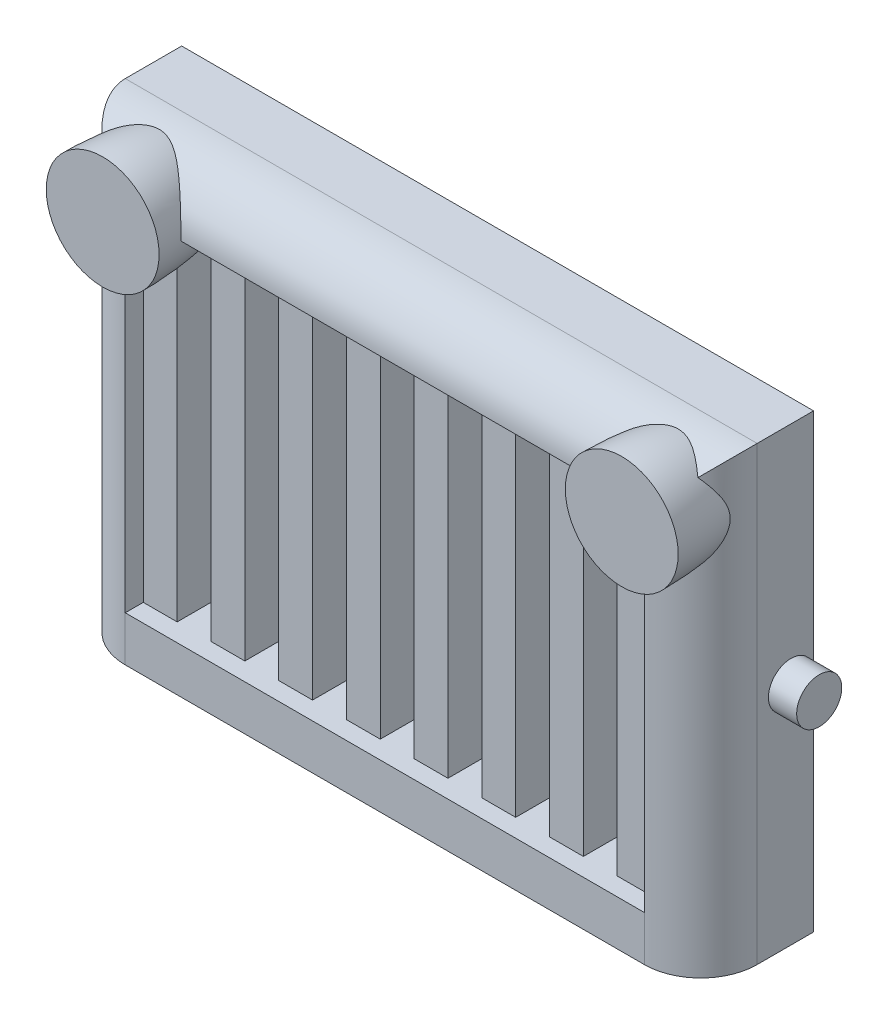
SolidWorks part; units mm, degrees
ref_plane "Front Plane" through (0, 0, 0) normal (0, 0, 1) x (1, 0, 0)
ref_plane "Top Plane" through (0, 0, 0) normal (0, 1, 0) x (1, 0, 0)
ref_plane "Right Plane" through (0, 0, 0) normal (1, 0, 0) x (0, 0, -1)
sketch "Sketch2" plane through (0, 0, 0) normal (0, 0, 1) x (1, 0, 0)
  line L1 (0, 0) -> (71.12, 0)
  line L2 (0, 0) -> (0, 50.8)
  line L3 (0, 50.8) -> (71.12, 50.8)
  line L4 (71.12, 0) -> (71.12, 50.8)
  dimension "D1" = 71.12
  dimension "D2" = 50.8
extrude "Boss-Extrude1" add sketch "Sketch2" along normal blind 12.7
fillet "Fillet2" radius 6.35 3 edges at (0, 25.4, 12.7) (71.12, 25.4, 12.7) (35.56, 50.8, 12.7)
sketch "Sketch3" plane through (0, 0, 12.7) normal (0, 0, 1) x (1, 0, 0)
  line L0 (64.77, 0) -> (64.77, 44.45) construction
  line L1 (6.35, 44.45) -> (64.77, 44.45)
  line L2 (6.35, 44.45) -> (6.35, 5.08)
  line L3 (6.35, 5.08) -> (64.77, 5.08)
  line L4 (64.77, 44.45) -> (64.77, 5.08)
  line L5 (6.35, 0) -> (64.77, 0) construction
  dimension "D1" = 5.08
extrude "Cut-Extrude1" cut sketch "Sketch3" against normal blind 6.35 contours L3 L4 L1 L2
sketch "Sketch4" plane through (0, 0, 6.35) normal (0, 0, 1) x (1, 0, 0)
  line L0 (6.35, 5.08) -> (64.77, 5.08) construction
  line L1 (6.35, 44.45) -> (10.16, 44.45)
  line L2 (6.35, 44.45) -> (6.35, 5.08)
  line L3 (6.35, 5.08) -> (10.16, 5.08)
  line L4 (10.16, 44.45) -> (10.16, 5.08)
  dimension "D1" = 3.81
extrude "Boss-Extrude2" add sketch "Sketch4" along normal blind 4.318
pattern_linear "LPattern1" count 8 spacing 7.62 along (1, 0, 0) of "Boss-Extrude2"
sketch "Sketch7" plane through (6.35, 0, 0) normal (1, 0, 0) x (0, 0, -1)
  line L3 (6.2189, 44.45) -> (-15.24, 44.45)
  line L4 (-15.24, 50.8) -> (-15.24, 44.45)
  arc A0 (-15.24, 50.8) -> (6.2189, 44.45) centre (-15.24, 11.3665) cw
  dimension "D1" = 6.35
  dimension "D2" = 0
revolve "Revolve1" add sketch "Sketch7" angle 360 about L3
sketch "Sketch9" plane through (0, 0, 0) normal (0, 0, -1) x (-1, 0, 0)
  line L0 (0, 0) -> (-71.12, 0) construction
  line L1 (-69.85, 15.875) -> (-1.27, 15.875)
  line L2 (-69.85, 15.875) -> (-69.85, 3.175)
  line L3 (-69.85, 3.175) -> (-1.27, 3.175)
  line L4 (-1.27, 15.875) -> (-1.27, 3.175)
  line L5 (-71.12, 0) -> (-71.12, 50.8) construction
  dimension "D1" = 12.7
  dimension "D2" = 3.175
  dimension "D3" = 68.58
  dimension "D4" = 1.27
extrude "Cut-Extrude3" cut sketch "Sketch9" against normal blind 5.08
ref_plane "Plane1" through (35.56, 0, 0) normal (1, 0, 0) x (0, 0, -1)
sketch "Sketch10" plane through (0, 0, 0) normal (-1, 0, 0) x (0, 0, 1)
  line L0 (0, 50.8) -> (0, 0) construction
  line L1 (6.35, 0) -> (0, 0) construction
  circle A0 centre (2.54, 25.4) radius 2.54
  dimension "D1" = 5.08
  dimension "D2" = 2.54
  dimension "D3" = 25.4
extrude "Boss-Extrude3" add sketch "Sketch10" along normal blind 3.175
mirror "Mirror1" about plane through (35.56, 0, 0) normal (1, 0, 0) of "Boss-Extrude3", "Revolve1"
sketch "Sketch8" plane through (0, 0, 0) normal (-1, 0, 0) x (0, 0, 1)
  line L1 (0, 50.8) -> (-30.144, 50.8)
  line L2 (0, 50.8) -> (0, -1.9259)
  line L3 (0, -1.9259) -> (-30.144, -1.9259)
  line L4 (-30.144, 50.8) -> (-30.144, -1.9259)
extrude "Cut-Extrude2" cut sketch "Sketch8" against normal blind 83.82
